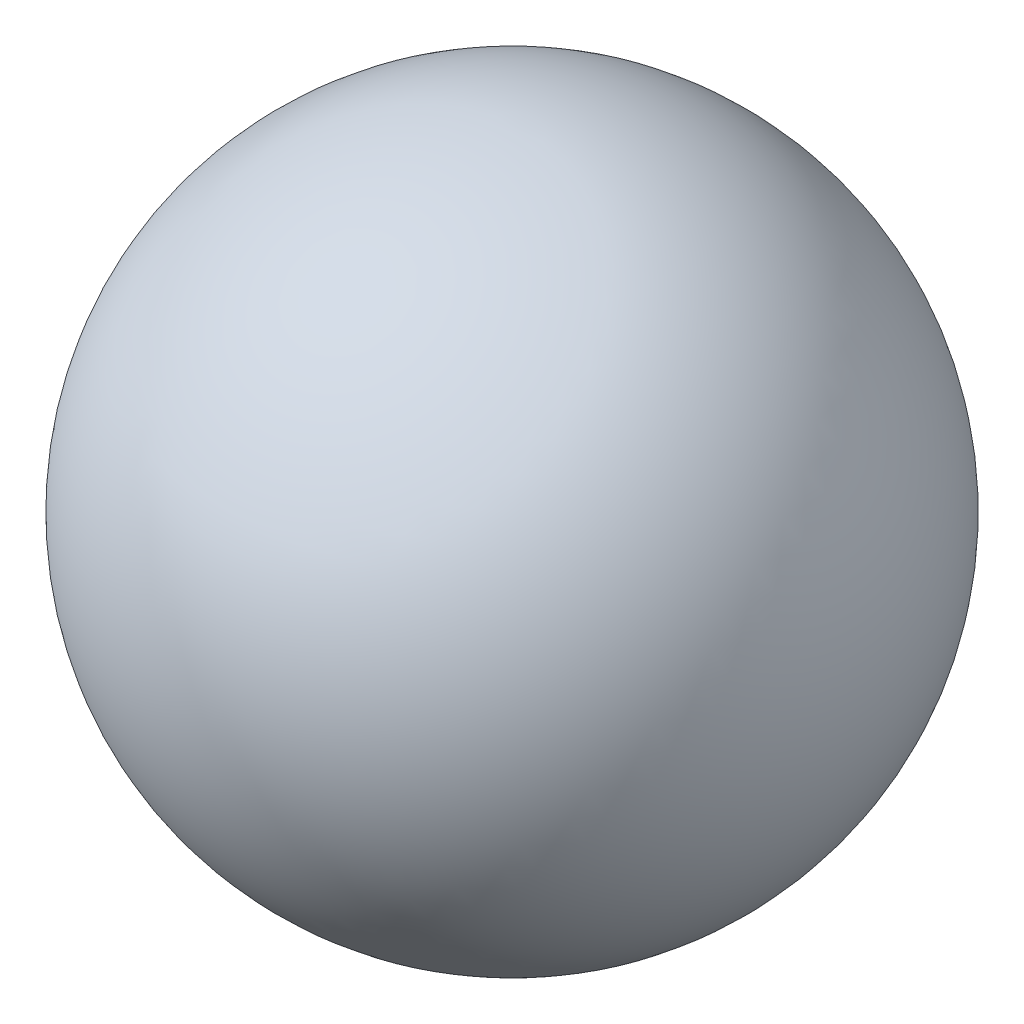
SolidWorks part; units mm, degrees
ref_plane "Face" through (0, 0, 0) normal (0, 0, 1) x (1, 0, 0)
ref_plane "Dessus" through (0, 0, 0) normal (0, 1, 0) x (1, 0, 0)
ref_plane "Droite" through (0, 0, 0) normal (1, 0, 0) x (0, 0, -1)
sketch "Esquisse1" plane through (0, 0, 0) normal (0, 0, 1) x (1, 0, 0)
  line L0 (0, 23.2957) -> (0, -25.0055) construction
  line L1 (0, 6.25) -> (0, -6.25)
  arc A0 (0, 6.25) -> (0, -6.25) centre (0, 0) ccw
  dimension "D1" = 6.25
revolve "Révolution1" add sketch "Esquisse1" angle 360 about L0
